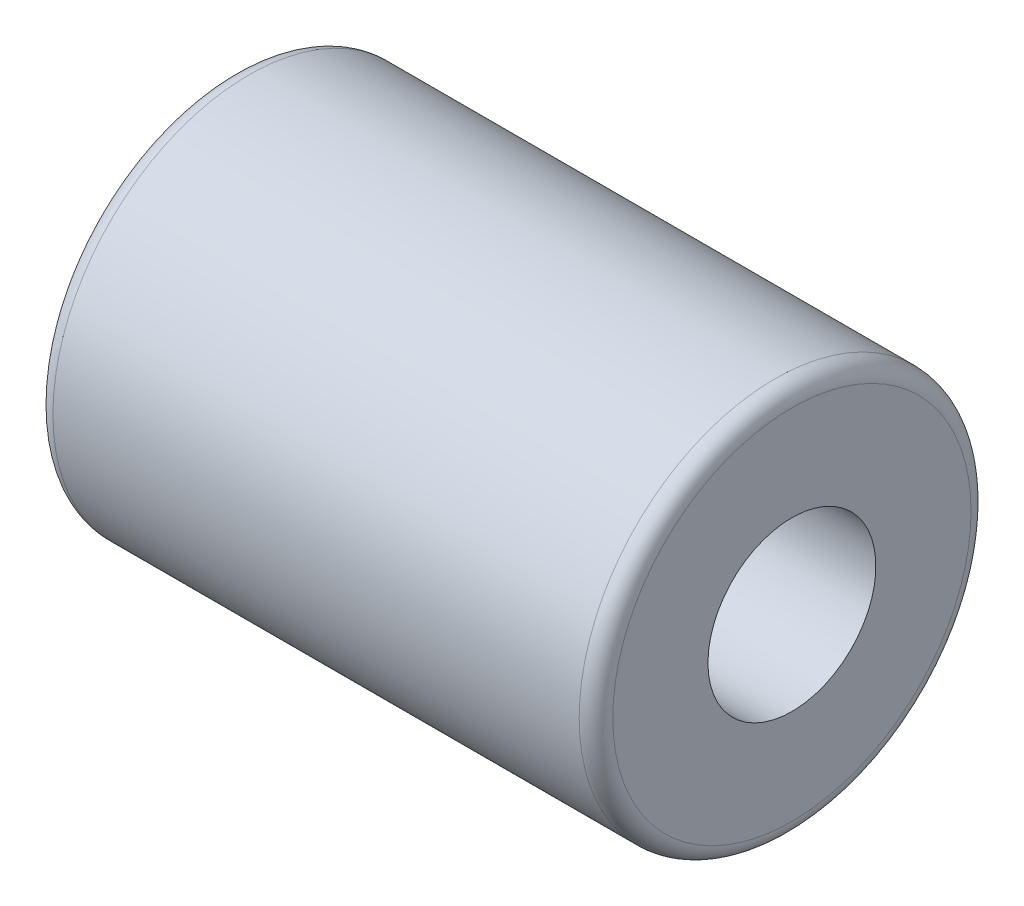
SolidWorks part; units mm, degrees
ref_plane "Front Plane" through (0, 0, 0) normal (0, 0, 1) x (1, 0, 0)
ref_plane "Top Plane" through (0, 0, 0) normal (0, 1, 0) x (1, 0, 0)
ref_plane "Right Plane" through (0, 0, 0) normal (1, 0, 0) x (0, 0, -1)
sketch "Sketch1" plane through (0, 0, 0) normal (0, 0, 1) x (1, 0, 0)
  line L0 (0, 0) -> (10, 0) construction
  line L2 (10, 1.5) -> (0, 1.5)
  line L3 (10, 1.5) -> (10, 3.5)
  line L4 (10, 3.5) -> (0, 3.5)
  line L5 (0, 1.5) -> (0, 3.5)
  dimension "D" = 7
  dimension "DR_s" = 3
  dimension "L" = 10
revolve "Revolve1" add sketch "Sketch1" angle 360 about L0
fillet "Fillet1" radius 0.3 2 edges at (0, 0, 3.5) (10, 0, 3.5)
sketch "Sketch2" plane through (0, 0, 0) normal (0, 0, 1) x (1, 0, 0)
  line L0 (10, 0) -> (0, 0) construction
  line L2 (5, 5) -> (5, 0) construction
  line L6 (9, 5) -> (10.1, 5)
  line L7 (9, 5) -> (9, 4.8)
  line L8 (9, 4.8) -> (10.1, 4.8)
  line L9 (10.1, 5) -> (10.1, 4.8)
  line L10 (-0.1, 5) -> (1, 5)
  line L11 (-0.1, 5) -> (-0.1, 4.8)
  line L12 (-0.1, 4.8) -> (1, 4.8)
  line L13 (1, 5) -> (1, 4.8)
  dimension "D1." = 9.6
  dimension "B" = 8
  dimension "W" = 1.1
  dimension "L" = 10
  dimension "D" = 10
revolve "Cut-Revolve1" [suppressed] cut sketch "Sketch2" angle 360 about L0
sketch "Sketch5" [suppressed] plane through (0, 0, 0) normal (0, 0, 1) x (1, 0, 0)
  line L0 (0, 0) -> (16, 0) construction
  line L1 (7.6127, 6) -> (8.3873, 6)
  line L2 (8, 6) -> (8, 0) construction
  arc A0 (7.6127, 6) -> (8.3873, 6) centre (8, 6.1) ccw
  dimension "R" = 0.4
  dimension "L" = 16
  dimension "D" = 12
  dimension "F_s" = 0.3
revolve "Cut-Revolve2" [suppressed] cut sketch "Sketch5" angle 360 about L0
sketch "Sketch6" [suppressed] plane through (0, 0, 0) normal (0, 0, 1) x (1, 0, 0)
  line L0 (0, 0) -> (34, 0) construction
  line L2 (34, 5) -> (5, 5)
  line L3 (34, 5) -> (34, 9.5)
  line L4 (34, 9.5) -> (5, 9.5)
  line L5 (5, 5) -> (5, 9.5)
  dimension "D" = 19
  dimension "DR_s" = 10
  dimension "L1" = 29
  dimension "V" = 5
revolve "Revolve2" [suppressed] add sketch "Sketch6" angle 360 about L0
fillet "Fillet3" [suppressed] radius 0.4
sketch "Sketch7" [suppressed] plane through (0, 0, 0) normal (0, 0, 1) x (1, 0, 0)
  line L0 (15, 0) -> (0, 0) construction
  line L2 (5, 9.5) -> (5, 0) construction
  line L6 (14.7, 9.5) -> (15.8, 9.5)
  line L7 (14.7, 9.5) -> (14.7, 9)
  line L8 (14.7, 9) -> (15.8, 9)
  line L9 (15.8, 9.5) -> (15.8, 9)
  line L10 (-5.8, 9.5) -> (-4.7, 9.5)
  line L11 (-5.8, 9.5) -> (-5.8, 9)
  line L12 (-5.8, 9) -> (-4.7, 9)
  line L13 (-4.7, 9.5) -> (-4.7, 9)
  dimension "D1." = 18
  dimension "B" = 19.4
  dimension "W" = 1.1
  dimension "L" = 15
  dimension "D" = 19
  dimension "KSS_2" = 5
revolve "Cut-Revolve3" [suppressed] cut sketch "Sketch7" angle 360 about L0
sketch "Sketch4" [suppressed] plane through (0, 0, 0) normal (0, 0, 1) x (1, 0, 0)
  line L0 (0, 0) -> (39, 0) construction
  line L3 (34, 9.5) -> (39, 9.5)
  line L4 (34, 9.5) -> (34, 5)
  line L5 (34, 5) -> (39, 5)
  line L6 (39, 9.5) -> (39, 5)
  line L7 (0, 9.5) -> (5, 9.5)
  line L8 (0, 9.5) -> (0, 5)
  line L9 (0, 5) -> (5, 5)
  line L10 (5, 9.5) -> (5, 5)
  dimension "V" = 5
  dimension "L1" = 29
  dimension "L" = 39
  dimension "D" = 19
  dimension "DR_S" = 10
revolve "Revolve3" [suppressed] add sketch "Sketch4" angle 360 about L0
equation "\"KSS_2@Sketch7\" = \"L@Sketch1\" / 2"
